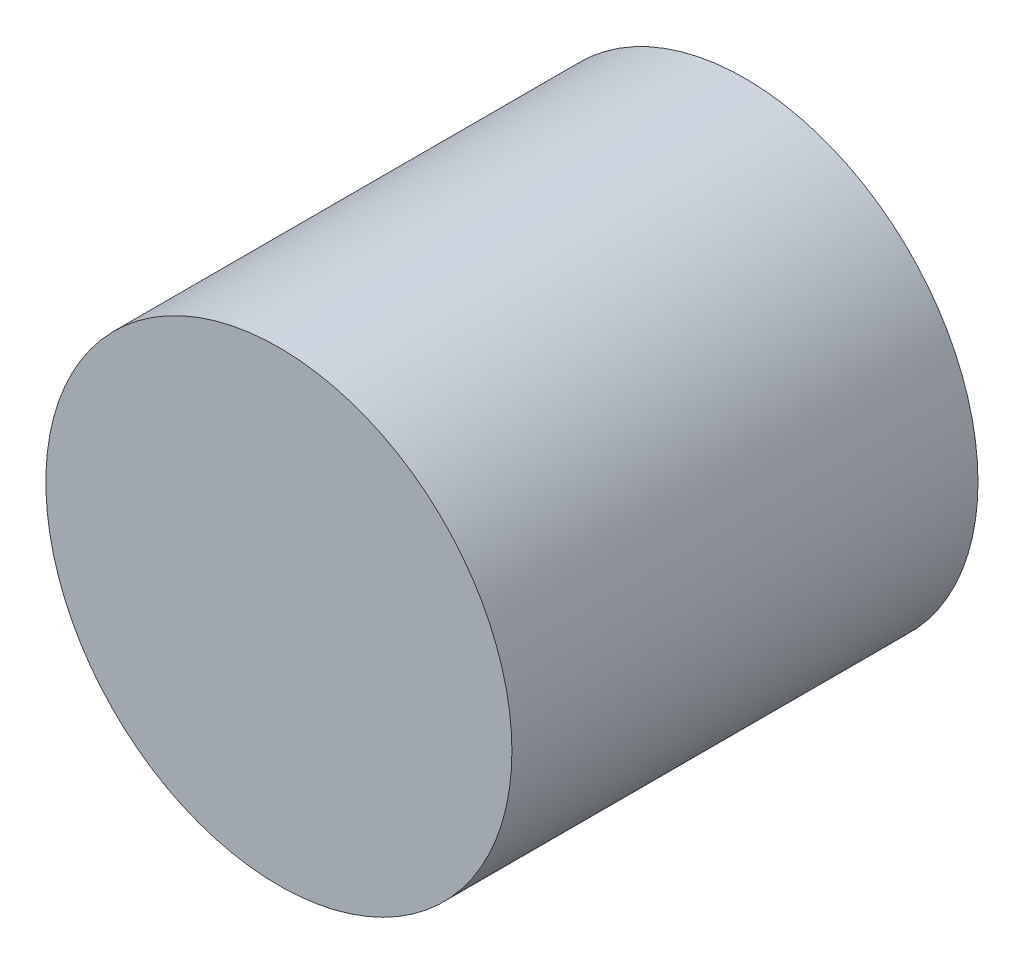
SolidWorks part; units mm, degrees
ref_plane "Front Plane" through (0, 0, 0) normal (0, 0, 1) x (1, 0, 0)
ref_plane "Top Plane" through (0, 0, 0) normal (0, 1, 0) x (1, 0, 0)
ref_plane "Right Plane" through (0, 0, 0) normal (1, 0, 0) x (0, 0, -1)
sketch "Sketch1" plane through (0, 0, 0) normal (0, 0, 1) x (1, 0, 0)
  circle A0 centre (0, 0) radius 5
  dimension "D1" = 10
extrude "Boss-Extrude1" add sketch "Sketch1" along normal blind 10
